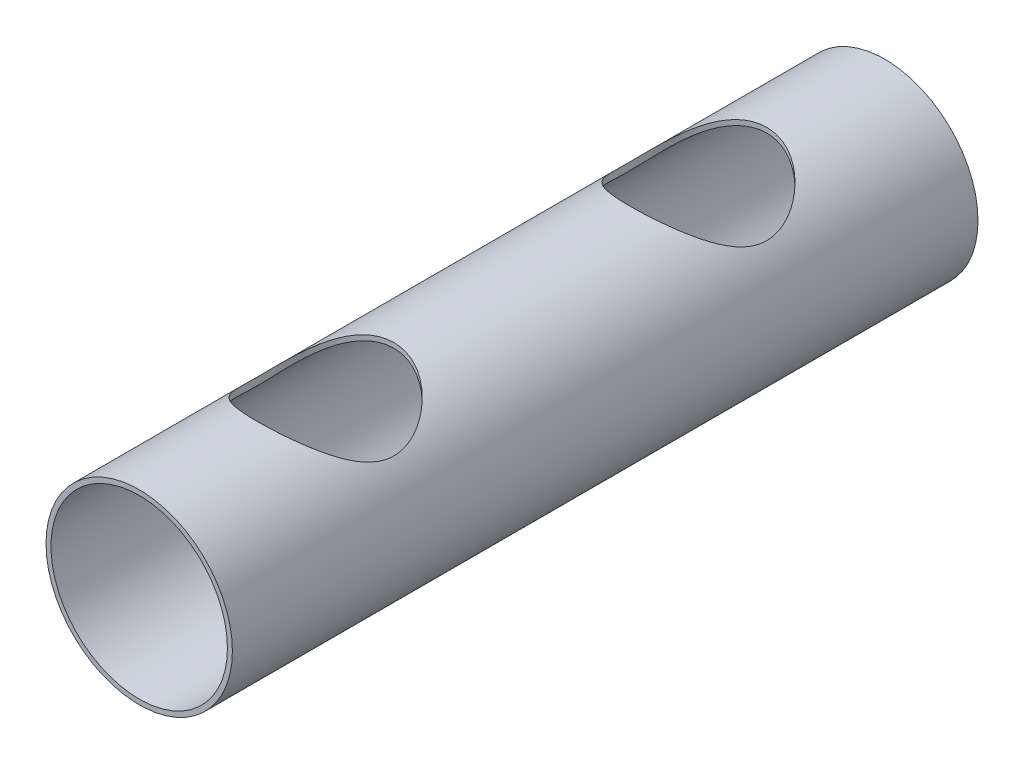
SolidWorks part; units mm, degrees
material "PVC Rigid"
ref_plane "Front Plane" through (0, 0, 0) normal (0, 0, 1) x (1, 0, 0)
ref_plane "Top Plane" through (0, 0, 0) normal (0, 1, 0) x (1, 0, 0)
ref_plane "Right Plane" through (0, 0, 0) normal (1, 0, 0) x (0, 0, -1)
sketch "Sketch1" plane through (0, 0, 0) normal (0, 0, 1) x (1, 0, 0)
  circle A0 centre (0, 0) radius 37.5
  circle A1 centre (0, 0) radius 35.5
  dimension "75" = 75
  dimension "D2" = 2
extrude "Boss-Extrude1" add sketch "Sketch1" along normal blind 300
sketch "Sketch2" plane through (0, 0, 0) normal (0, 1, 0) x (1, 0, 0)
  line L0 (0, -75) -> (0, -225) construction
  line L1 (35.5, 0) -> (-35.5, 0) construction
  line L3 (0, 0) -> (0, -75) construction
  circle A0 centre (0, -75) radius 27.5
  circle A1 centre (0, -225) radius 27.5
  dimension "D2" = 55
  dimension "D1" = 75
  dimension "D3" = 150
extrude "Cut-Extrude1" cut sketch "Sketch2" along normal blind 100
